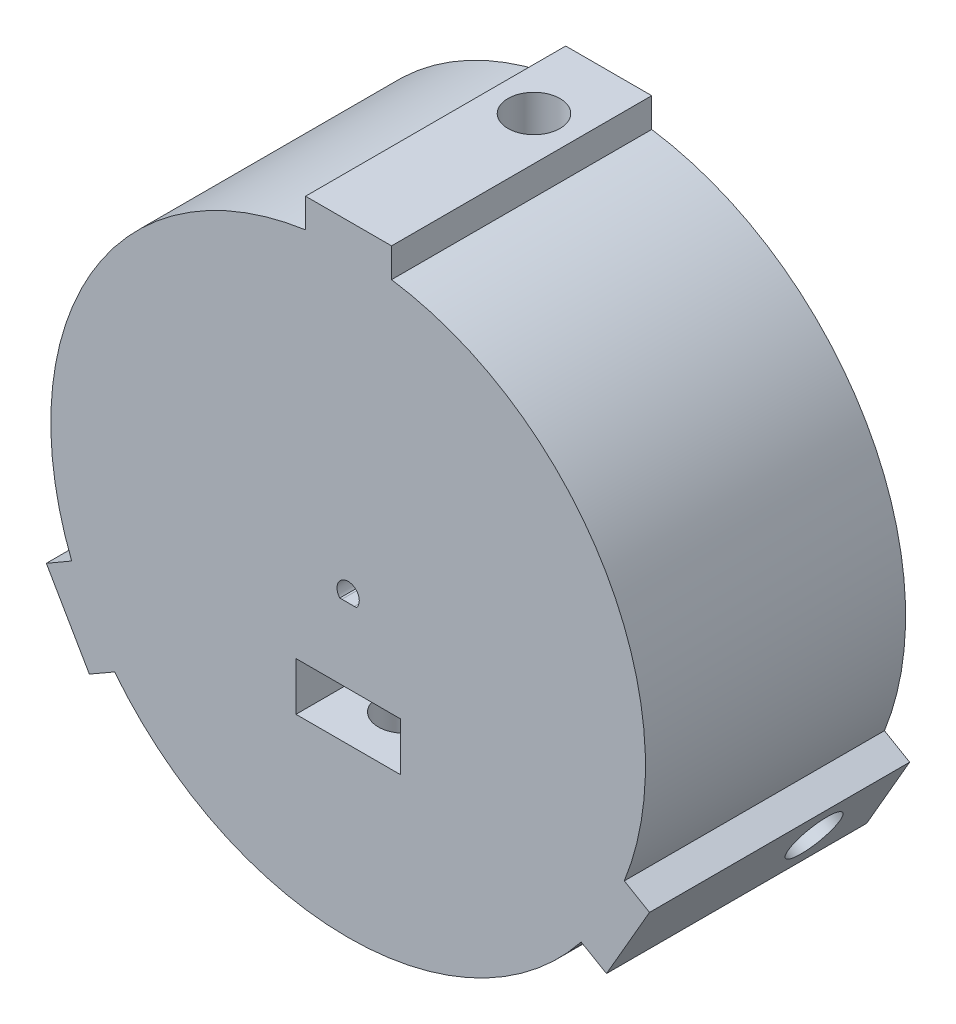
SolidWorks part; units mm, degrees
ref_plane "Front Plane" through (0, 0, 0) normal (0, 0, 1) x (1, 0, 0)
ref_plane "Top Plane" through (0, 0, 0) normal (0, 1, 0) x (1, 0, 0)
ref_plane "Right Plane" through (0, 0, 0) normal (1, 0, 0) x (0, 0, -1)
sketch "Sketch2" plane through (0, 0, 0) normal (0, 0, 1) x (1, 0, 0)
  circle A0 centre (0, 0) radius 40
  dimension "D1" = 80
extrude "Boss-Extrude1" add sketch "Sketch2" along normal blind 35
sketch "Sketch3" plane through (0, 0, 0) normal (0, 0, -1) x (-1, 0, 0)
  line L0 (-4, 39) -> (-4, 4)
  line L1 (-4, 4) -> (4, 4)
  line L2 (4, 4) -> (4, 39)
  line L3 (4, 39) -> (-4, 39)
  line L4 (31.775, -22.9641) -> (35.775, -16.0359)
  line L5 (35.775, -16.0359) -> (5.4641, 1.4641)
  line L6 (5.4641, 1.4641) -> (1.4641, -5.4641)
  line L7 (1.4641, -5.4641) -> (31.775, -22.9641)
  line L8 (-35.775, -16.0359) -> (-31.775, -22.9641)
  line L9 (-31.775, -22.9641) -> (-1.4641, -5.4641)
  line L10 (-1.4641, -5.4641) -> (-5.4641, 1.4641)
  line L11 (-5.4641, 1.4641) -> (-35.775, -16.0359)
  point P16 (0, 0)
  dimension "D1" = 4
  dimension "D2" = 8
  dimension "D3" = 35
  dimension "D4" = 4
  dimension "D5" = 3
extrude "Cut-Extrude1" cut sketch "Sketch3" against normal blind 20 contours L3 L0 L1 L2 | L8 L9 L10 L11 | L4 L5 L6 L7
sketch "Sketch4" plane through (-3.4641, -2, 0) normal (-0.866, -0.5, 0) x (0, 0, 1)
  line L0 (20, 4) -> (20, -4) construction
  line L1 (0, 4) -> (0, -4) construction
  line L2 (20, 4) -> (20, -4)
  line L3 (0, 4) -> (0, -4)
  circle A0 centre (10, 0) radius 3.5
  dimension "D1" = 7
  dimension "D2" = 10
  dimension "D3" = 8
  dimension "D4" = 4
extrude "Cut-Extrude2" cut sketch "Sketch4" along normal blind 80 contours A0
sketch "Sketch5" plane through (0, 4, 0) normal (0, 1, 0) x (1, 0, 0)
  line L0 (4, 0) -> (-4, 0) construction
  line L1 (4, -20) -> (-4, -20) construction
  line L2 (4, 0) -> (-4, 0)
  line L3 (4, -20) -> (-4, -20)
  circle A0 centre (0, -10) radius 3.5
  dimension "D1" = 7
  dimension "D2" = 10
extrude "Cut-Extrude3" cut sketch "Sketch5" along normal blind 50 contours A0
sketch "Sketch6" plane through (3.4641, -2, 0) normal (0.866, -0.5, 0) x (0, 0, -1)
  line L0 (-20, -4) -> (-20, 4) construction
  line L1 (0, -4) -> (0, 4) construction
  line L2 (-20, -4) -> (-20, 4)
  line L3 (0, -4) -> (0, 4)
  circle A0 centre (-10, 0) radius 3.5
  point P6 (-20, 0)
  dimension "D1" = 7
  dimension "D2" = 10
  dimension "D3" = 0
extrude "Cut-Extrude4" cut sketch "Sketch6" along normal blind 50 contours A0
sketch "Sketch8" plane through (0, 0, 0) normal (0, 0, -1) x (-1, 0, 0)
  line L0 (-32.9711, -10.8924) -> (-25.9519, -23.0501)
  line L1 (-32.9711, -10.8924) -> (-27.3419, -7.6424)
  line L2 (-27.3419, -7.6424) -> (-20.3227, -19.8001)
  line L3 (-20.3227, -19.8001) -> (-25.9519, -23.0501)
  line L4 (-35.775, -16.0359) -> (-31.775, -22.9641) construction
  line L5 (-35.775, -16.0359) -> (-31.775, -22.9641)
  line L6 (-6.986, 27.5) -> (-6.986, 34)
  line L7 (7.0524, 34) -> (-6.986, 34)
  line L8 (7.0524, 34) -> (7.0524, 27.5)
  line L9 (7.0524, 27.5) -> (-6.986, 27.5)
  line L10 (27.3087, -7.6999) -> (32.9379, -10.9499)
  line L11 (25.9186, -23.1076) -> (32.9379, -10.9499)
  line L12 (25.9186, -23.1076) -> (20.2895, -19.8576)
  line L13 (20.2895, -19.8576) -> (27.3087, -7.6999)
  point P17 (0, 0)
  dimension "D1" = 5
  dimension "D2" = 6.5
  dimension "D3" = 14.0384
  dimension "D4" = 3
extrude "Cut-Extrude5" cut sketch "Sketch8" against normal blind 15.5 contours L0 L3 L2 L1 | L9 L6 L7 L8 | L11 L10 L13 L12
sketch "Sketch11" plane through (0, 0, 20) normal (0, 0, -1) x (-1, 0, 0)
  line L0 (-4, 34) -> (4, 34)
  line L1 (4, 27.5) -> (4, 34) construction
  line L2 (4, 4) -> (4, 39) construction
  line L3 (4, 34) -> (4, 27.5)
  line L4 (4, 27.5) -> (-4, 27.5)
  line L5 (-4, 27.5) -> (-4, 34)
  line L6 (25.8157, -10.2859) -> (31.4449, -13.5359)
  line L7 (31.4449, -13.5359) -> (27.4449, -20.4641)
  line L8 (27.4449, -20.4641) -> (21.8157, -17.2141)
  line L9 (21.8157, -17.2141) -> (25.8157, -10.2859)
  line L10 (-21.8157, -17.2141) -> (-27.4449, -20.4641)
  line L11 (-27.4449, -20.4641) -> (-31.4449, -13.5359)
  line L12 (-31.4449, -13.5359) -> (-25.8157, -10.2859)
  line L13 (-25.8157, -10.2859) -> (-21.8157, -17.2141)
  point P21 (0, 0)
  dimension "D1" = 3
extrude "Boss-Extrude2" add sketch "Sketch11" along normal blind 4.5
sketch "Sketch12" plane through (0, 0, 15.5) normal (0, 0, -1) x (-1, 0, 0)
  line L0 (-6.986, 32.1) -> (7.0524, 32.1)
  line L1 (-6.986, 27.5) -> (-6.986, 34) construction
  line L2 (7.0524, 34) -> (7.0524, 27.5) construction
  line L3 (7.0524, 34) -> (4, 34) construction
  line L5 (-4, 34) -> (-6.986, 34) construction
  line L6 (7.0524, 34) -> (4, 34)
  line L8 (-4, 34) -> (-6.986, 34)
  line L9 (-6.986, 32.1) -> (-6.986, 34)
  line L10 (7.0524, 32.1) -> (7.0524, 34)
  line L11 (4, 34) -> (4, 39) construction
  line L12 (4, 39) -> (-4, 39) construction
  line L13 (-4, 39) -> (-4, 34) construction
  line L14 (4, 34) -> (4, 39)
  line L15 (4, 39) -> (-4, 39)
  line L16 (-4, 39) -> (-4, 34)
  line L17 (25.9186, -23.1076) -> (27.4449, -20.4641)
  line L18 (27.4449, -20.4641) -> (31.775, -22.9641)
  line L19 (31.775, -22.9641) -> (35.775, -16.0359)
  line L20 (35.775, -16.0359) -> (31.4449, -13.5359)
  line L21 (31.4449, -13.5359) -> (32.9379, -10.9499)
  line L22 (31.2924, -9.9999) -> (32.9379, -10.9499)
  line L23 (31.2924, -9.9999) -> (24.2732, -22.1576)
  line L24 (24.2732, -22.1576) -> (25.9186, -23.1076)
  line L25 (-32.9711, -10.8924) -> (-31.4449, -13.5359)
  line L26 (-31.4449, -13.5359) -> (-35.775, -16.0359)
  line L27 (-35.775, -16.0359) -> (-31.775, -22.9641)
  line L28 (-31.775, -22.9641) -> (-27.4449, -20.4641)
  line L29 (-27.4449, -20.4641) -> (-25.9519, -23.0501)
  line L30 (-24.3064, -22.1001) -> (-25.9519, -23.0501)
  line L31 (-24.3064, -22.1001) -> (-31.3256, -9.9424)
  line L32 (-31.3256, -9.9424) -> (-32.9711, -10.8924)
  point P30 (0, 0)
  dimension "D1" = 1.9
  dimension "D2" = 3
extrude "Boss-Extrude3" add sketch "Sketch12" along normal up to surface (15.5 mm away) up to face at (40, 0, 0)
sketch "Sketch13" plane through (0, 34, 0) normal (0, 1, 0) x (1, 0, 0)
  circle A0 centre (0, -10) radius 3.5 construction
  circle A1 centre (0, -10) radius 3.5
sketch "Sketch14" plane through (33.775, -19.5, 0) normal (0.866, -0.5, 0) x (0, 0, -1)
  circle A0 centre (-10, 0) radius 3.5 construction
  circle A1 centre (-10, 0) radius 3.5
sketch "Sketch15" plane through (-33.775, -19.5, 0) normal (-0.866, -0.5, 0) x (0, 0, 1)
  circle A0 centre (10, 0) radius 3.5 construction
  circle A1 centre (10, 0) radius 3.5
sketch "Sketch17" plane through (0, 0, 0) normal (0, 0, -1) x (-1, 0, 0)
  line L0 (-5.8428, 32.8975) -> (-5.8428, 43.5095)
  line L5 (-5.8428, 43.5095) -> (5.7278, 43.5095)
  line L6 (5.7278, 43.5095) -> (5.7548, 32.8975)
  line L10 (-5.8428, 32.8975) -> (5.7548, 32.8975)
  line L11 (31.4114, -11.3887) -> (25.6127, -21.4325)
  line L12 (34.8164, -26.7152) -> (25.6127, -21.4325)
  line L13 (40.6018, -16.6948) -> (34.8164, -26.7152)
  line L14 (31.4114, -11.3887) -> (40.6018, -16.6948)
  line L15 (-25.5686, -21.5087) -> (-31.3674, -11.465)
  line L16 (-40.5443, -16.7943) -> (-31.3674, -11.465)
  line L17 (-34.759, -26.8148) -> (-40.5443, -16.7943)
  line L18 (-25.5686, -21.5087) -> (-34.759, -26.8148)
  point P22 (0, 0)
  dimension "D1" = 3
extrude "Boss-Extrude4" add sketch "Sketch17" against normal up to surface (35 mm away) up to face at (40, 0, 35)
sketch "Sketch18" plane through (-37.6804, -21.7548, 0) normal (-0.866, -0.5, 0) x (0, 0, 1)
  circle A0 centre (10, 0) radius 3.5 construction
  circle A1 centre (10, 0) radius 3.5
extrude "Cut-Extrude9" cut sketch "Sketch18" against normal mid plane 50
sketch "Sketch19" plane through (37.6804, -21.7548, 0) normal (0.866, -0.5, 0) x (0, 0, -1)
  circle A0 centre (-10, 0) radius 3.5 construction
  circle A1 centre (-10, 0) radius 3.5
extrude "Cut-Extrude10" cut sketch "Sketch19" against normal mid plane 50
sketch "Sketch20" plane through (0, 43.5095, 0) normal (0, 1, 0) x (1, 0, 0)
  circle A0 centre (0, -10) radius 3.5 construction
  circle A1 centre (0, -10) radius 3.5
extrude "Cut-Extrude11" cut sketch "Sketch20" against normal mid plane 50
sketch "Sketch21" plane through (0, 0, 0) normal (0, 0, -1) x (-1, 0, 0)
  line L1 (4, 4) -> (4, 27.5) construction
  line L3 (4, 22.4) -> (9.1, 22.4)
  line L4 (4, 4) -> (4, 27.5) construction
  line L6 (4, 4) -> (4, 22.4)
  line L8 (4, 4) -> (4, 22.4)
  line L9 (4, 22.4) -> (9.1, 22.4)
  line L10 (4, 4) -> (9.1, 4)
  line L11 (9.1, 22.4) -> (9.1, 4)
  line L12 (7.0524, 27.5) -> (4, 27.5) construction
  dimension "D1" = 18.4
  dimension "D2" = 5.1
  dimension "D3" = 5.1
extrude "Cut-Extrude12" cut sketch "Sketch21" against normal blind 13
sketch "Sketch22" plane through (0, 0, 0) normal (0, 0, -1) x (-1, 0, 0)
  line L0 (4, 4) -> (4, 17.3)
  line L1 (4, 4) -> (4, 27.5) construction
  line L2 (4, 17.3) -> (9.1, 17.3)
  line L3 (9.1, 22.4) -> (9.1, 4) construction
  line L4 (9.1, 17.3) -> (9.1, 4)
  line L5 (9.1, 4) -> (4, 4)
  line L6 (4, 22.4) -> (9.1, 22.4) construction
  line L7 (-1.0859, -9.8808) -> (1.4641, -5.4641)
  line L8 (1.4641, -5.4641) -> (12.9822, -12.1141)
  line L9 (12.9822, -12.1141) -> (10.4322, -16.5308)
  line L10 (10.4322, -16.5308) -> (-1.0859, -9.8808)
  line L11 (-8.0141, 5.8808) -> (-5.4641, 1.4641)
  line L12 (-5.4641, 1.4641) -> (-16.9822, -5.1859)
  line L13 (-16.9822, -5.1859) -> (-19.5322, -0.7692)
  line L14 (-19.5322, -0.7692) -> (-8.0141, 5.8808)
  point P23 (0, 0)
  dimension "D1" = 5.1
  dimension "D2" = 3
sketch "Sketch23" plane through (0, 0, 0) normal (0, 0, -1) x (-1, 0, 0)
  line L0 (4, 4) -> (4, 22.4)
  line L1 (4, 22.4) -> (9.1, 22.4)
  line L2 (9.1, 22.4) -> (9.1, 4)
  line L3 (9.1, 4) -> (4, 4)
  line L4 (-1.0859, -9.8808) -> (1.4641, -5.4641)
  line L5 (1.4641, -5.4641) -> (17.399, -14.6641)
  line L6 (17.399, -14.6641) -> (14.849, -19.0808)
  line L7 (14.849, -19.0808) -> (-1.0859, -9.8808)
  line L8 (-8.0141, 5.8808) -> (-5.4641, 1.4641)
  line L9 (-5.4641, 1.4641) -> (-21.399, -7.7359)
  line L10 (-21.399, -7.7359) -> (-23.949, -3.3192)
  line L11 (-23.949, -3.3192) -> (-8.0141, 5.8808)
  point P18 (0, 0)
  dimension "D1" = 3
extrude "Cut-Extrude13" cut sketch "Sketch23" against normal blind 13
extrude "Boss-Extrude5" add sketch "Sketch22" against normal blind 7.9
sketch "Sketch24" plane through (0, 0, 35) normal (0, 0, 1) x (1, 0, 0)
  line L0 (0.8316, -1) -> (1.1181, -0.9999)
  line L1 (-1.1181, -0.9999) -> (-0.8313, -1)
  line L2 (0.8316, -1) -> (-0.8313, -1)
  arc A0 (1.1181, -0.9999) -> (-1.5, 0) centre (0, 0) ccw
  arc A1 (-1.5, 0) -> (-1.1181, -0.9999) centre (0, 0) ccw
  dimension "D1" = 0
extrude "Cut-Extrude14" cut sketch "Sketch24" against normal blind 8.5
sketch "Sketch25" plane through (0, 0, 0) normal (0, 0, -1) x (-1, 0, 0)
  circle A0 centre (0, 0) radius 9
  dimension "D1" = 18
extrude "Cut-Extrude15" cut sketch "Sketch25" against normal up to surface (20 mm away) up to face at (-13.6399, -7.875, 20)
sketch "Sketch27" plane through (0, 0, 35) normal (0, 0, 1) x (1, 0, 0)
  line L0 (-7.0183, -17.5) -> (-7.0183, -11)
  line L1 (7.0201, -11) -> (-7.0183, -11)
  line L2 (7.0201, -11) -> (7.0201, -17.5)
  line L3 (7.0201, -17.5) -> (-7.0183, -17.5)
  line L4 (-0.8313, -1) -> (0.8316, -1) construction
  point P6 (0.0001, -1)
  dimension "D1" = 10
  dimension "D2" = 14.0384
  dimension "D3" = 7.02
extrude "Cut-Extrude16" cut sketch "Sketch27" against normal blind 13
sketch "Sketch28" plane through (0, -17.5, 0) normal (0, 1, 0) x (1, 0, 0)
  line L3 (-7.0183, -35) -> (7.0201, -35) construction
  line L7 (-7.0183, -35) -> (7.0201, -35)
  line L8 (-7.0183, -22) -> (7.0201, -22) construction
  line L9 (-7.0183, -22) -> (7.0201, -22)
  circle A0 centre (0, -27.44) radius 3.5
  point P2 (0, -24.1609)
  dimension "D1" = 5.44
extrude "Cut-Extrude18" cut sketch "Sketch28" against normal blind 50 and the other way blind 18 contours A0
